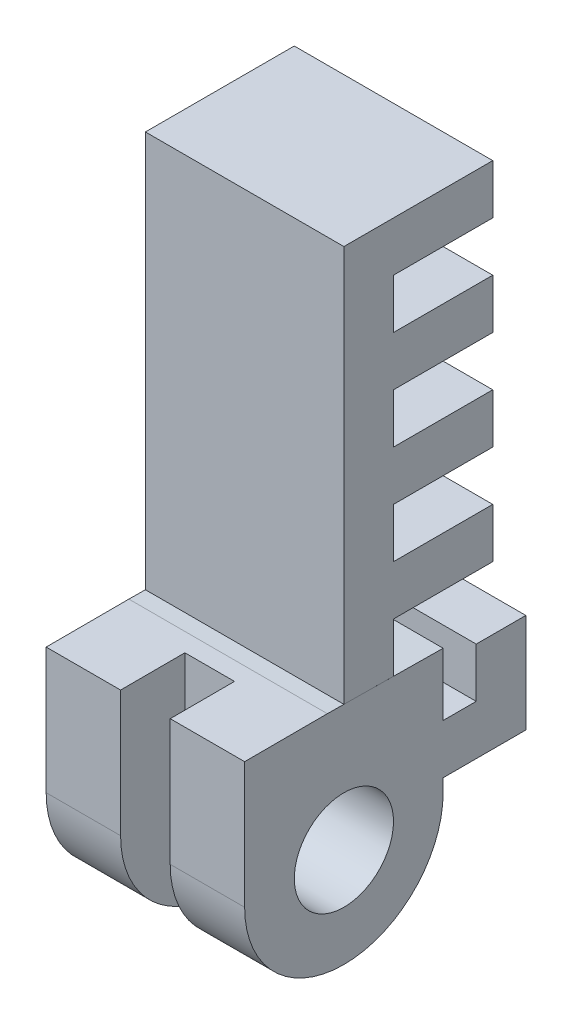
SolidWorks part; units mm, degrees
ref_plane "Front Plane" through (0, 0, 0) normal (0, 0, 1) x (1, 0, 0)
ref_plane "Top Plane" through (0, 0, 0) normal (0, 1, 0) x (1, 0, 0)
ref_plane "Right Plane" through (0, 0, 0) normal (1, 0, 0) x (0, 0, -1)
sketch "Sketch3" plane through (0, 0, 0) normal (1, 0, 0) x (0, 0, -1)
  line L0 (108.2758, -67.2745) -> (108.2758, -83.2745)
  line L1 (113.7758, -67.2745) -> (113.7758, -77.2745)
  line L2 (108.2758, -83.2745) -> (119.7758, -83.2745)
  line L3 (119.7758, -77.2745) -> (119.7758, -83.2745)
  line L5 (113.7758, -77.2745) -> (119.7758, -77.2745)
  line L7 (119.7758, -83.2745) -> (119.8877, -83.3049)
  line L10 (108.2758, -67.2745) -> (113.7758, -67.2745)
sketch "Sketch4" plane through (0, 0, 0) normal (1, 0, 0) x (0, 0, -1)
  line L0 (114.8897, -68.2659) -> (117.8896, -68.2972)
  line L1 (117.8896, -68.2972) -> (120.9259, -68.3288)
  line L4 (121.8896, -68.3388) -> (120.9259, -68.3288)
  line L5 (109.8896, -68.2775) -> (114.8897, -68.2659)
  line L6 (109.8896, -75.9036) -> (109.8896, -68.2775)
  line L8 (121.8896, -75.9036) -> (121.8896, -68.3388)
  circle A0 centre (115.8896, -75.9036) radius 3
  arc A1 (109.8896, -75.9036) -> (121.8896, -75.9036) centre (115.8896, -75.9036) ccw
extrude "Boss-Extrude2" add sketch "Sketch4" against normal blind 12 from offset 0
sketch "Sketch5" plane through (0, 0, 0) normal (1, 0, 0) x (0, 0, -1)
  line L0 (115.8896, -44.3064) -> (115.8896, -68.2763)
  line L1 (121.8896, -68.3388) -> (114.8897, -68.2659) construction
  line L2 (118.8895, -68.3064) -> (118.8895, -65.3064)
  line L3 (118.8895, -65.3064) -> (124.8895, -65.3064)
  line L4 (124.8895, -65.3064) -> (124.8895, -62.3064)
  line L5 (124.8895, -62.3064) -> (118.8895, -62.3064)
  line L6 (115.8896, -68.2763) -> (118.8895, -68.3064)
  line L8 (118.8895, -62.3064) -> (118.8895, -59.3064)
  line L9 (118.8895, -59.3064) -> (124.8895, -59.3064)
  line L10 (124.8895, -59.3064) -> (124.8895, -56.3064)
  line L11 (124.8895, -56.3064) -> (118.8895, -56.3064)
  line L12 (118.8895, -56.3064) -> (118.8895, -53.3064)
  line L13 (118.8895, -53.3064) -> (124.8895, -53.3064)
  line L14 (124.8895, -53.3064) -> (124.8895, -50.3064)
  line L15 (124.8895, -50.3064) -> (118.8895, -50.3064)
  line L16 (118.8895, -50.3064) -> (118.8895, -47.3064)
  line L18 (118.8895, -47.3064) -> (124.8895, -47.3064)
  line L19 (124.8895, -47.3064) -> (124.8895, -44.3064)
  line L20 (124.8895, -44.3064) -> (115.8896, -44.3064)
extrude "Boss-Extrude3" add sketch "Sketch5" against normal blind 12
extrude "Cut-Extrude1" cut sketch "Sketch3" against normal blind 3 from offset 4.5 offset against normal yes
sketch "Sketch7" plane through (0, 0, 0) normal (1, 0, 0) x (0, 0, -1)
  line L0 (121.8896, -72.1212) -> (123.8896, -72.1212)
  line L1 (121.8896, -75.9036) -> (121.8896, -68.3388) construction
  line L2 (123.8896, -72.1212) -> (123.8896, -69.1212)
  line L3 (123.8896, -69.1212) -> (126.8896, -69.1212)
  line L4 (126.8896, -69.1212) -> (126.8896, -75.1212)
  line L5 (126.8896, -75.1212) -> (121.8896, -75.1212)
  line L6 (121.8896, -72.1212) -> (121.8896, -75.1212)
extrude "Boss-Extrude4" add sketch "Sketch7" against normal blind 12
